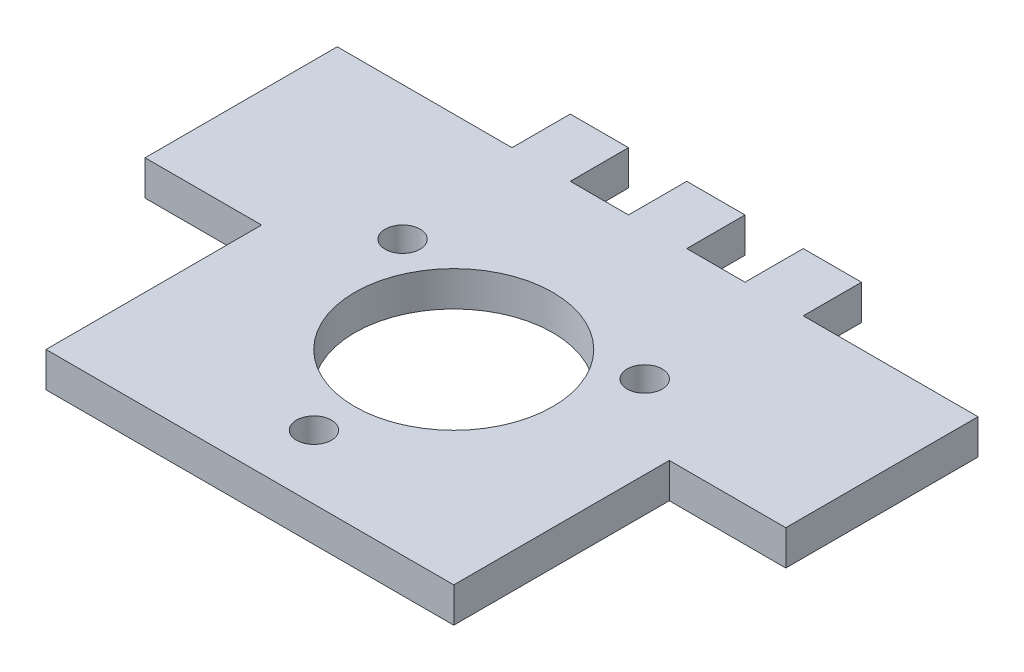
SolidWorks part; units mm, degrees
material "Balsa"
ref_plane "Plan de face" through (0, 0, 0) normal (0, 0, 1) x (1, 0, 0)
ref_plane "Plan de dessus" through (0, 0, 0) normal (0, 1, 0) x (1, 0, 0)
ref_plane "Plan de droite" through (0, 0, 0) normal (1, 0, 0) x (0, 0, -1)
sketch "Esquisse1" plane through (0, 0, 0) normal (0, 1, 0) x (1, 0, 0)
  line L1 (-17.5, 17.5) -> (17.5, 17.5)
  line L2 (-17.5, 17.5) -> (-17.5, -17.5)
  line L3 (-17.5, -17.5) -> (17.5, -17.5)
  line L4 (17.5, 17.5) -> (17.5, -17.5)
  dimension "D3" = 17.5
  dimension "D1" = 35
  dimension "D2" = 35
  dimension "D4" = 17.5
extrude "Boss.-Extru.1" add sketch "Esquisse1" along normal blind 3
sketch "Esquisse2" plane through (0, 3, 0) normal (0, 1, 0) x (1, 0, 0)
  line L1 (17.5, 17.5) -> (-17.5, 17.5) construction
  line L2 (-12.5, 17.5) -> (-7.5, 17.5)
  line L3 (-12.5, 17.5) -> (-12.5, 22.5)
  line L4 (-12.5, 22.5) -> (-7.5, 22.5)
  line L5 (-7.5, 17.5) -> (-7.5, 22.5)
  line L6 (-17.5, 17.5) -> (-17.5, -17.5) construction
  dimension "D1" = 5
  dimension "D2" = 5
  dimension "D3" = 5
extrude "Boss.-Extru.2" add sketch "Esquisse2" against normal blind 3
pattern_linear "Répétition linéaire1" count 3 spacing 10 along (1, 0, 0) of "Boss.-Extru.2"
sketch "Esquisse3" plane through (0, 3, 0) normal (0, 1, 0) x (1, 0, 0)
  line L0 (0, 3.9506) -> (0, -20.3145) construction
  circle A0 centre (0, 0) radius 8.5
  circle A1 centre (0, -12) radius 1.5
  circle A2 centre (-10.3923, 6) radius 1.5
  circle A3 centre (10.3923, 6) radius 1.5
  point P11 (0, 0)
  dimension "D1" = 17
  dimension "D2" = 3
  dimension "D3" = 12
  dimension "D5" = 0
  dimension "D4" = 3
extrude "Enlèv. mat.-Extru.1" cut sketch "Esquisse3" against normal blind 5
sketch "Esquisse4" plane through (0, 3, 0) normal (0, 1, 0) x (1, 0, 0)
  line L0 (-17.5, 17.5) -> (-17.5, -17.5) construction
  line L1 (-17.5, 17.5) -> (-27.5, 17.5)
  line L2 (-17.5, 17.5) -> (-17.5, 1)
  line L3 (-17.5, 1) -> (-27.5, 1)
  line L4 (-27.5, 17.5) -> (-27.5, 1)
  dimension "D1" = 1
  dimension "D2" = 16.5
  dimension "D3" = 10
extrude "Boss.-Extru.3" add sketch "Esquisse4" against normal up to surface (3 mm away) up to face at (10.3923, 0, -4.5)
mirror "Symétrie1" about plane through (0, 0, 0) normal (1, 0, 0) of "Boss.-Extru.3"
